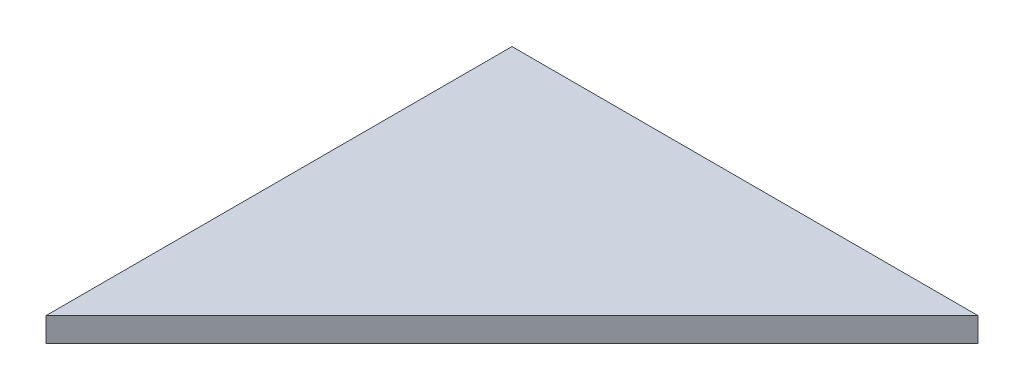
SolidWorks part; units mm, degrees
material "Acrylic (Medium-high impact)"
ref_plane "Front Plane" through (0, 0, 0) normal (0, 0, 1) x (1, 0, 0)
ref_plane "Top Plane" through (0, 0, 0) normal (0, 1, 0) x (1, 0, 0)
ref_plane "Right Plane" through (0, 0, 0) normal (1, 0, 0) x (0, 0, -1)
ref_plane "Plane1" through (0, -113.7049, 0) normal (0, -1, 0) x (-1, 0, 0)
sketch "Sketch1" plane through (0, -113.7049, 0) normal (0, -1, 0) x (-1, 0, 0)
  line L0 (-107.5728, -49.6381) -> (-49.6381, -107.5728) construction
  line L1 (-49.6381, -107.5728) -> (-49.6381, -49.6381) construction
  line L2 (-49.6381, -49.6381) -> (-107.5728, -49.6381) construction
  line L3 (-107.5728, -49.6381) -> (-49.6381, -107.5728)
  line L4 (-49.6381, -107.5728) -> (-49.6381, -49.6381)
  line L5 (-49.6381, -49.6381) -> (-107.5728, -49.6381)
extrude "Boss-Extrude1" add sketch "Sketch1" against normal mid plane 3
ref_plane "Plane2" through (80.4015, -80.4015, 0) normal (0.7071, -0.7071, 0) x (-0.7071, -0.7071, 0)
